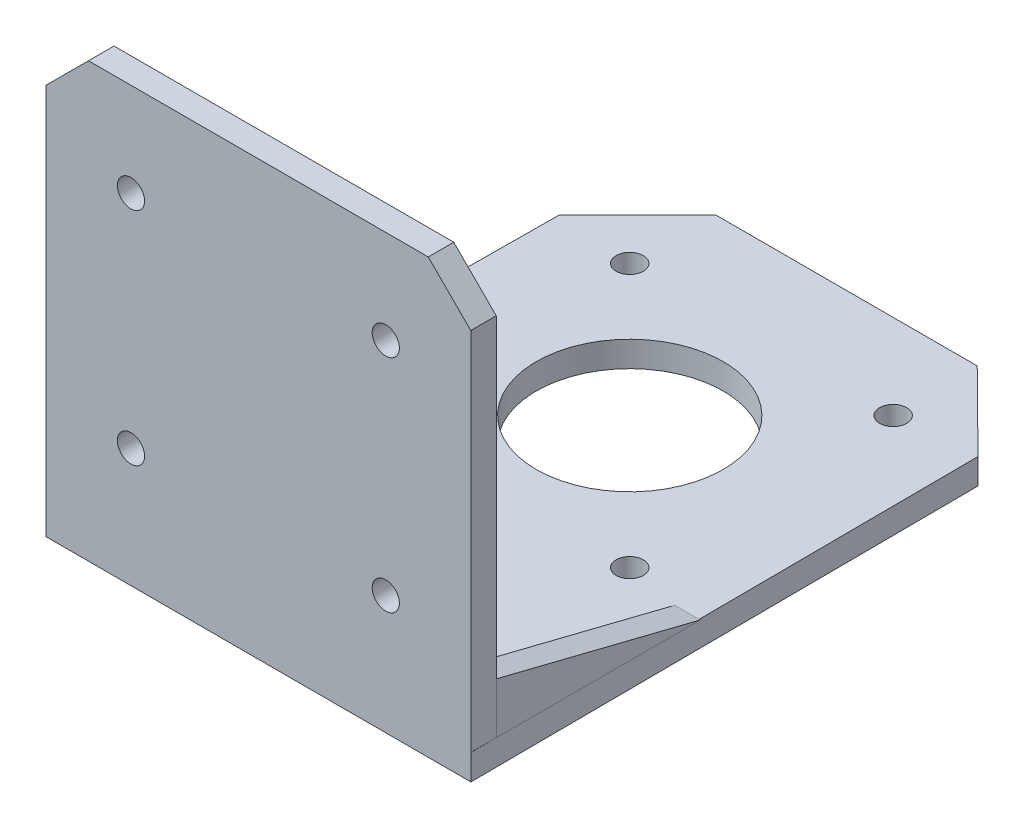
SolidWorks part; units mm, degrees
material "PLA"
ref_plane "Front Plane" through (0, 0, 0) normal (0, 0, 1) x (1, 0, 0)
ref_plane "Top Plane" through (0, 0, 0) normal (0, 1, 0) x (1, 0, 0)
ref_plane "Right Plane" through (0, 0, 0) normal (1, 0, 0) x (0, 0, -1)
sketch "Sketch2" plane through (0, 0, 0) normal (0, 1, 0) x (1, 0, 0)
  line L3 (-0.2811, -64.6895) -> (-50.2811, -64.6895)
  line L5 (-49.8637, -4.6901) -> (-50.2811, -64.6895)
  line L6 (-49.8637, -4.6901) -> (-40.6727, 4.5009)
  line L7 (-9.8894, 4.5009) -> (-40.6727, 4.5009)
  line L8 (-0.6074, -4.6895) -> (-0.2811, -64.6895)
  line L9 (-9.8894, 4.5009) -> (-0.6074, -4.6895)
  line L10 (-25.2811, 4.5009) -> (-25.2811, -64.6895) construction
  line L11 (-0.4801, -21) -> (-53.4702, -21) construction
  circle A0 centre (-25.2811, -21) radius 11
  circle A1 centre (-40.7811, -5.5) radius 1.6
  circle A2 centre (-9.7811, -5.5) radius 1.6
  circle A3 centre (-40.7811, -36.5) radius 1.6
  circle A4 centre (-9.7811, -36.5) radius 1.6
  dimension "D3" = 15.5
  dimension "D1" = 50
  dimension "D2" = 4.6895
  dimension "D4" = 15.5
  dimension "D5" = 15.5
  dimension "D6" = 15.5
  dimension "D7" = 15.5
  dimension "D8" = 21
  dimension "D9" = 60
  dimension "D10" = 15.5
  dimension "D11" = 15.5
  dimension "D12" = 15.5
extrude "Boss-Extrude1" add sketch "Sketch2" along normal blind 3
sketch "Sketch4" plane through (0, 3, 0) normal (0, 1, 0) x (1, 0, 0)
  line L0 (-0.2811, -64.6895) -> (-0.6074, -4.6895) construction
  line L1 (-50.2811, -64.6895) -> (-0.2974, -64.6895)
  line L2 (-50.2811, -64.6895) -> (-50.2811, -61.6895)
  line L3 (-50.2811, -61.6895) -> (-0.2974, -61.6895)
  line L4 (-0.2974, -64.6895) -> (-0.2974, -61.6895)
extrude "Boss-Extrude2" add sketch "Sketch4" along normal blind 48
sketch "Sketch5" plane through (0, 0, 61.6895) normal (0, 0, -1) x (-1, 0, 0)
  line L0 (0.2974, 51) -> (0.2974, 46)
  line L1 (0.2974, 51) -> (0.2974, 3) construction
  line L2 (0.2974, 46) -> (5.2974, 51)
  line L3 (0.2974, 51) -> (50.2811, 51) construction
  line L4 (5.2974, 51) -> (0.2974, 51)
  line L5 (50.2811, 51) -> (45.2811, 51)
  line L6 (45.2811, 51) -> (50.2811, 46)
  line L7 (50.2811, 51) -> (50.2811, 3) construction
  line L8 (50.2811, 46) -> (50.2811, 51)
  dimension "D1" = 5
  dimension "D2" = 5
  dimension "D3" = 5
  dimension "D4" = 5
extrude "Cut-Extrude1" cut sketch "Sketch5" against normal blind 8
hole_wizard "Ø3.2 (3.2) Diameter Hole1" positions "Sketch8" profile "Sketch9" hole size "Ø3.2" standard "ANSI Metric"
sketch "Sketch8" plane through (0, 0, 61.6895) normal (0, 0, -1) x (-1, 0, 0)
  line L0 (5.2974, 51) -> (45.2811, 51) construction
  line L1 (0.2974, 3) -> (50.2602, 3) construction
  line L2 (50.2811, 46) -> (50.2811, 3) construction
  line L3 (50.2811, 46) -> (50.2811, 3) construction
  line L4 (0.2974, 46) -> (0.2974, 3) construction
  point P0 (10.2974, 40)
  point P2 (40.2811, 40)
  point P4 (40.2811, 14)
  point P6 (10.2974, 14)
  dimension "D1" = 11
  dimension "D2" = 11
  dimension "D3" = 11
  dimension "D4" = 11
  dimension "D5" = 10
  dimension "D6" = 10
  dimension "D7" = 10
  dimension "D8" = 10
sketch "Sketch9" plane through (-10.2974, 40, 61.6895) normal (1, 0, 0) x (0, 1, 0)
  line L0 (0, 0) -> (0, 4.1614)
  line L1 (0, 4.1614) -> (1.6, 3.2)
  line L2 (1.6, 3.2) -> (1.6, 0)
  line L5 (1.6, 0) -> (0, 0)
  line L10 (0, 4.1614) -> (-1.6, 3.2) construction
  line L11 (0, -6.35) -> (0, 107.95) construction
  dimension "Hole Dia." = 3.2
  dimension "Hole Depth" = 3.2
  dimension "Drill Angle" = 118
other "Gusset1" parameters "D1"=3, "D2"=3, "D3"=0, "D4"=0, "D10"=5, "D11"=24, "D12"=6, "D13"=15, "D14"=45, "D15"=15, "D16"=5, "D17"=5, "D18"=45
sketch "Sketch10" plane through (-50.2602, 3, 61.6895) normal (1, 0, 0) x (0, 0, -1)
  line L0 (0, 0) -> (24, 0)
  line L1 (0, 0) -> (0, 6)
  line L2 (24, 0) -> (0, 6)
other "Gusset2" parameters "D1"=3, "D2"=3, "D3"=0, "D4"=0, "D10"=5, "D11"=6, "D12"=24, "D13"=15, "D14"=45, "D15"=15, "D16"=5, "D17"=5, "D18"=45
sketch "Sketch11" plane through (-0.2974, 3, 61.6895) normal (-1, 0, 0) x (0, 0, 1)
  line L0 (0, 0) -> (0, 6)
  line L1 (0, 0) -> (-24, 0)
  line L2 (0, 6) -> (-24, 0)
